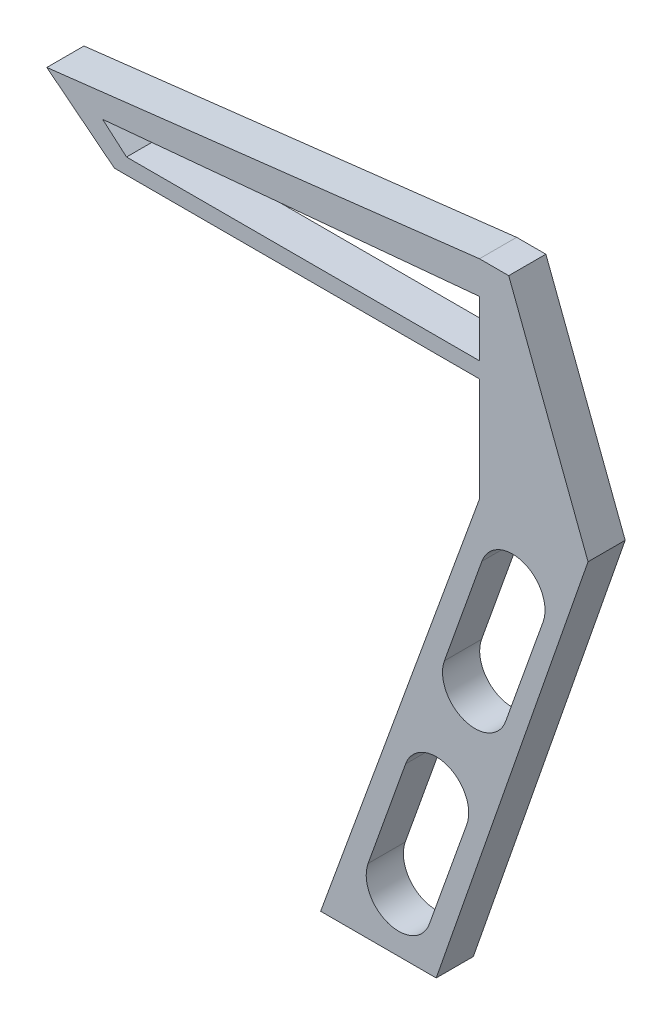
SolidWorks part; units mm, degrees
ref_plane "Plan de face" through (0, 0, 0) normal (0, 0, 1) x (1, 0, 0)
ref_plane "Plan de dessus" through (0, 0, 0) normal (0, 1, 0) x (1, 0, 0)
ref_plane "Plan de droite" through (0, 0, 0) normal (1, 0, 0) x (0, 0, -1)
sketch "Esquisse1" plane through (0, 0, 0) normal (0, 0, 1) x (1, 0, 0)
  line L0 (0, 0) -> (0, -64.4777)
  line L1 (0, -64.4777) -> (-85.505, -299.4009)
  line L2 (0, 0) -> (0, 30)
  line L3 (0, 30) -> (-202.861, 11.1377)
  line L4 (-202.861, 11.1377) -> (-190, 0)
  line L5 (0, 47.5629) -> (15.7425, 47.5629)
  line L6 (-207.234, 0) -> (-196.5337, -8.4574)
  line L7 (0, 47.5629) -> (-232.9112, 20.295)
  line L8 (-232.9112, 20.295) -> (-207.234, 0)
  line L9 (-68.158, -299.4009) -> (-23.2963, -299.4009)
  line L10 (24.0022, -81.2751) -> (-46.5588, -278.8473) construction
  line L11 (17.7853, -98.6826) -> (-2.3948, -155.1872) construction
  line L12 (-68.158, -299.4009) -> (-85.505, -299.4009)
  line L13 (-196.5337, -8.4574) -> (0, -8.4574)
  line L14 (-190, 0) -> (0, 0)
  line L16 (58.4426, -64.4777) -> (15.7425, 47.5629)
  line L17 (34.2658, -104.5684) -> (14.0857, -161.073)
  line L18 (1.3048, -92.7968) -> (-18.8753, -149.3013)
  line L19 (-23.2963, -213.712) -> (-43.4764, -270.2166) construction
  line L20 (-6.8158, -219.5978) -> (-26.9959, -276.1024)
  line L21 (-39.7768, -207.8261) -> (-59.9569, -264.3307)
  line L22 (-23.2963, -299.4009) -> (58.4426, -64.4777)
  arc A0 (34.2658, -104.5684) -> (1.3048, -92.7968) centre (17.7853, -98.6826) ccw
  arc A1 (-18.8753, -149.3013) -> (14.0857, -161.073) centre (-2.3948, -155.1872) ccw
  arc A2 (-6.8158, -219.5978) -> (-39.7768, -207.8261) centre (-23.2963, -213.712) ccw
  arc A3 (-59.9569, -264.3307) -> (-26.9959, -276.1024) centre (-43.4764, -270.2166) ccw
  point P20 (7.6952, -126.9349)
  point P25 (-33.3864, -241.9643)
extrude "Boss.-Extru.1" add sketch "Esquisse1" along normal blind 20
